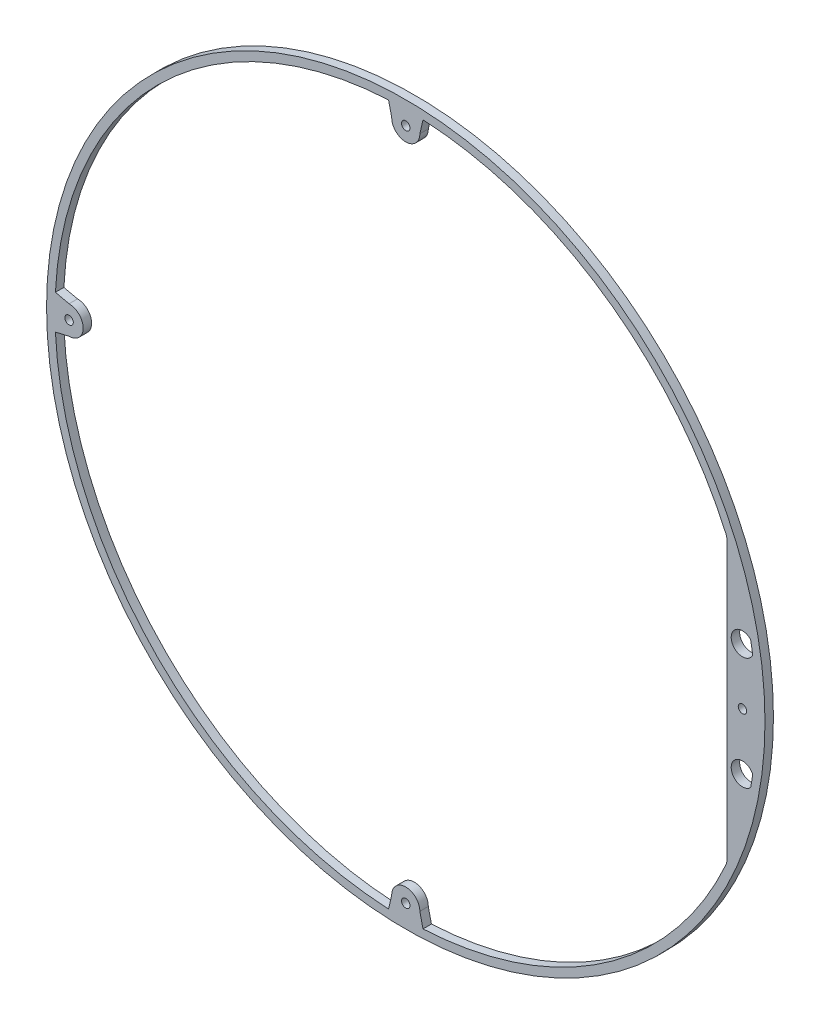
SolidWorks part; units mm, degrees
ref_plane "Front Plane" through (0, 0, 0) normal (0, 0, 1) x (1, 0, 0)
ref_plane "Top Plane" through (0, 0, 0) normal (0, 1, 0) x (1, 0, 0)
ref_plane "Right Plane" through (0, 0, 0) normal (1, 0, 0) x (0, 0, -1)
sketch "Sketch1" plane through (0, 0, 0) normal (0, 0, 1) x (1, 0, 0)
  circle A1 centre (0, 0) radius 124.525
  circle A2 centre (0, 0) radius 127.525
  circle A6 centre (0, 0) radius 127.525
  dimension "D2" = 3
  dimension "D1" = 1
extrude "Boss-Extrude1" add sketch "Sketch1" along normal blind 3
sketch "Sketch2" plane through (0, 0, 3) normal (0, 0, 1) x (1, 0, 0)
  line L0 (-5, 119.525) -> (-6.1102, 124.375)
  line L1 (5, 119.525) -> (6.1102, 124.375)
  line L2 (119.525, 5) -> (124.375, 6.1102)
  line L3 (119.525, -5) -> (124.375, -6.1102)
  line L4 (5, -119.525) -> (6.1102, -124.375)
  line L5 (-5, -119.525) -> (-6.1102, -124.375)
  line L6 (-119.525, -5) -> (-124.375, -6.1102)
  line L7 (-119.525, 5) -> (-124.375, 6.1102)
  arc A0 (-5, 119.525) -> (5, 119.525) centre (0, 119.525) ccw
  circle A1 centre (0, 0) radius 124.525 construction
  arc A2 (-6.1102, 124.375) -> (-124.375, 6.1102) centre (0, 0) ccw
  arc A3 (119.525, 5) -> (119.525, -5) centre (119.525, 0) ccw
  arc A4 (5, -119.525) -> (-5, -119.525) centre (0, -119.525) ccw
  arc A5 (-119.525, -5) -> (-119.525, 5) centre (-119.525, 0) ccw
  circle A6 centre (0, 119.525) radius 1.5
  circle A7 centre (119.525, 0) radius 1.5
  circle A8 centre (0, -119.525) radius 1.5
  circle A9 centre (-119.525, 0) radius 1.5
  arc A10 (-124.375, -6.1102) -> (-6.1102, -124.375) centre (0, 0) ccw
  circle A11 centre (0, 0) radius 127.525
  circle A12 centre (0, 0) radius 127.525
  arc A13 (6.1102, -124.375) -> (124.375, -6.1102) centre (0, 0) ccw
  arc A14 (124.375, 6.1102) -> (6.1102, 124.375) centre (0, 0) ccw
  circle A15 centre (0, 0) radius 124.525
  point P14 (0, 0)
  point P22 (0, 0)
  point P40 (0, 0)
  circle M21 centre (0, 0) radius 124.525
  dimension "D1" = 10
  dimension "D3" = 3
  dimension "D5" = 4.85
  dimension "D6" = 0
  dimension "D2" = 4
  dimension "D4" = 4
  dimension "D7" = 4
extrude "Boss-Extrude2" add sketch "Sketch2" against normal up to surface (3 mm away) contours L0 A0 L1 A6 M21 | L6 A5 L7 A9 M21 | L4 A4 L5 A8 M21 | L2 A3 L3 A7 M21 up to face at (127.525, 0, 0)
sketch "Sketch3" plane through (0, 0, 3) normal (0, 0, 1) x (1, 0, 0)
  line L0 (114.0459, 50) -> (114.0459, -50)
  line L1 (119.525, 20) -> (119.525, -20)
  arc A0 (124.375, 6.1102) -> (6.1102, 124.375) centre (0, 0) ccw construction
  arc A1 (6.1102, -124.375) -> (124.375, -6.1102) centre (0, 0) ccw construction
  circle A2 centre (119.525, 20) radius 4
  circle A3 centre (119.525, -20) radius 4
  circle A4 centre (119.525, 0) radius 1.5 construction
  circle A5 centre (119.525, 0) radius 1.5
  arc M4 (6.1102, 124.375) -> (124.375, 6.1102) centre (0, 0) cw
  line M5 (124.375, 6.1102) -> (119.525, 5)
  arc M6 (119.525, 5) -> (119.525, -5) centre (119.525, 0) ccw
  line M7 (119.525, -5) -> (124.375, -6.1102)
  arc M8 (124.375, -6.1102) -> (6.1102, -124.375) centre (0, 0) cw
  dimension "D3" = 8
  dimension "D1" = 100
  dimension "D4" = 40
extrude "Boss-Extrude3" add sketch "Sketch3" against normal up to surface (3 mm away) contours A3 L1 A2 L0 M6 M4 M8 | A2 L1 M5 M4 | A3 L1 M8 M7 up to face at (127.525, 0, 0)
fillet "Fillet1" radius 5 2 edges at (114.0459, -50, 1.5) (114.0459, 50, 1.5)
equation "\"C\"=1"
equation "\"D1@Sketch1\"=\"C\""
equation "\"T\"=3"
equation "\"D1@Boss-Extrude1\"=\"T\""
equation "\"D1\"=100"
equation "\"D1@Sketch3\"=\"D1\""
equation "\"D2\"=40"
equation "\"D4@Sketch3\"=\"D2\""
equation "\"F\"=5"
equation "\"D1@Fillet1\"=\"F\""
